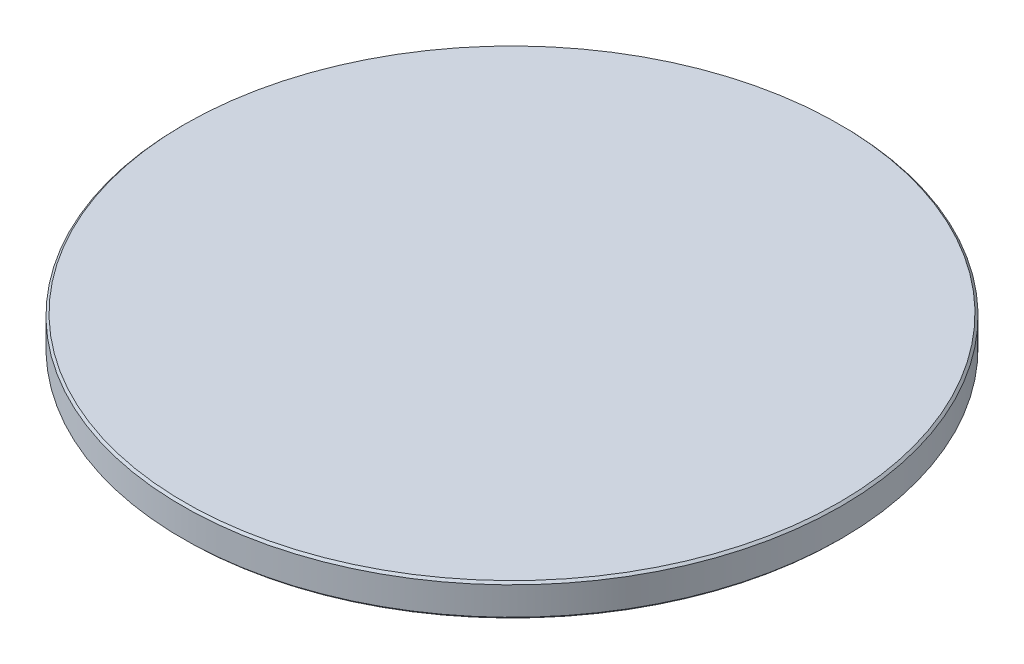
SolidWorks part; units mm, degrees
material "Borofloat"
ref_plane "Piano frontale" through (0, 0, 0) normal (0, 0, 1) x (1, 0, 0)
ref_plane "Piano superiore" through (0, 0, 0) normal (0, 1, 0) x (1, 0, 0)
ref_plane "Piano destro" through (0, 0, 0) normal (1, 0, 0) x (0, 0, -1)
sketch "Schizzo1" plane through (0, 0, 0) normal (0, 0, 1) x (1, 0, 0)
  line L0 (0, 3) -> (0, 0)
  line L1 (0, 3) -> (-30.3, 3)
  line L2 (0, 3) -> (0, 0) construction
  line L3 (0, 0) -> (-30.3, 0)
  line L4 (-30.5, 2.8) -> (-30.5, 0.2)
  line L5 (-30.3, 3) -> (-30.5, 2.8)
  line L6 (-30.5, 0.2) -> (-30.3, 0)
  point P1 (-30.5, 0)
  point P3 (-30.5, 3)
  dimension "D1" = 3
  dimension "D2" = 61
revolve "Rivoluzione1" add sketch "Schizzo1" angle 360 about L2
